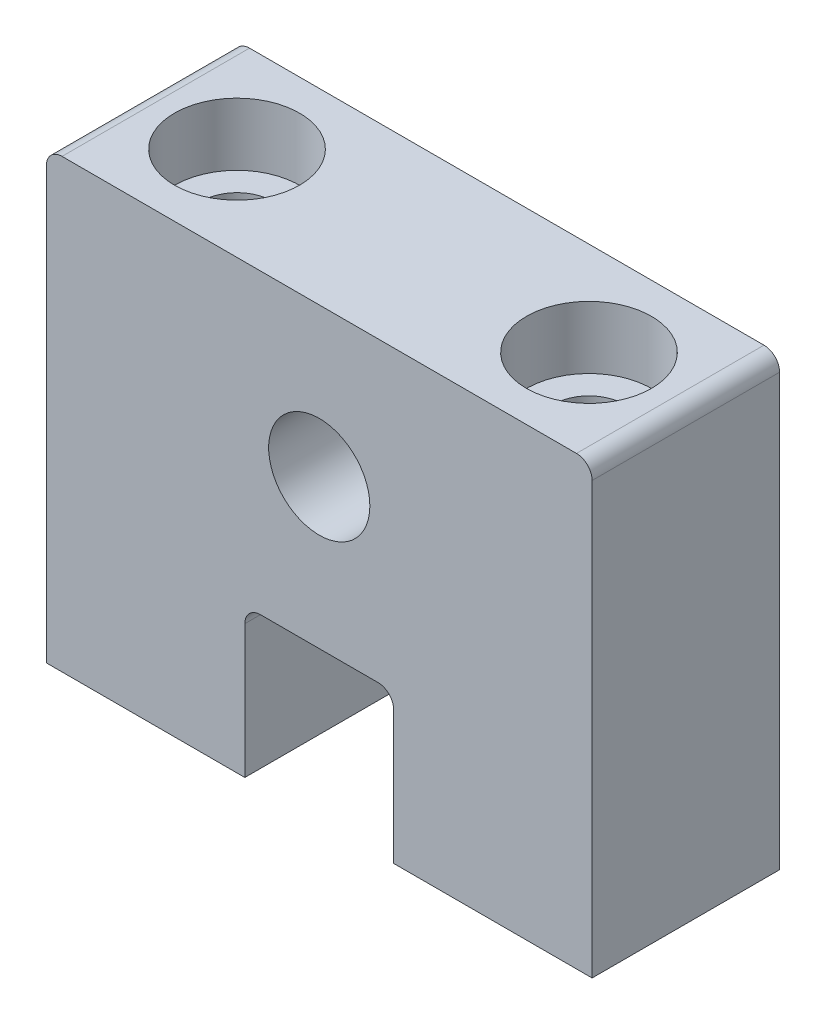
SolidWorks part; units mm, degrees
ref_plane "Front Plane" through (0, 0, 0) normal (0, 0, 1) x (1, 0, 0)
ref_plane "Top Plane" through (0, 0, 0) normal (0, 1, 0) x (1, 0, 0)
ref_plane "Right Plane" through (0, 0, 0) normal (1, 0, 0) x (0, 0, -1)
sketch "Sketch1" plane through (0, 0, 0) normal (0, 0, 1) x (1, 0, 0)
  line L0 (0, -26.1041) -> (0, 52.7781) construction
  line L1 (-17.4625, 28.575) -> (17.4625, 28.575)
  line L3 (-4.7625, 0) -> (-17.4625, 0)
  line L4 (17.4625, 0) -> (17.4625, 28.575)
  line L6 (-4.7625, 0) -> (-4.7625, 9.525)
  line L7 (-17.4625, 0) -> (-17.4625, 28.575)
  line L8 (4.7625, 0) -> (17.4625, 0)
  line L9 (-4.7625, 9.525) -> (4.7625, 9.525)
  line L10 (4.7625, 0) -> (4.7625, 9.525)
  circle A0 centre (0, 19.05) radius 3.2385
  point P15 (0, 15.8115)
  point P23 (4.7625, 4.7625)
  dimension "D6" = 6.477
  dimension "D3" = 9.525
  dimension "D2" = 19.05
  dimension "D1" = 28.575
  dimension "D4" = 9.525
  dimension "D7" = 34.925
extrude "Boss-Extrude1" add sketch "Sketch1" along normal blind 12
sketch "Sketch2" plane through (0, 28.575, 0) normal (0, 1, 0) x (1, 0, 0)
  line L0 (4.7625, -12) -> (4.7625, 0) construction
  line L1 (-4.7625, -12) -> (-4.7625, 0) construction
  line L2 (4.7625, -12) -> (4.7625, 0)
  line L3 (-4.7625, -12) -> (-4.7625, 0)
  line L4 (0, 0) -> (0, -12) construction
  line L5 (17.4625, 0) -> (-17.4625, 0) construction
  line L6 (17.4625, -12) -> (-17.4625, -12) construction
  line L7 (-17.4625, -6) -> (17.4625, -6) construction
  line L8 (-17.4625, -12) -> (-17.4625, 0) construction
  line L9 (17.4625, -12) -> (17.4625, 0) construction
  point P0 (-11.2625, -6)
  point P1 (11.2625, -6)
  dimension "D1" = 6.5
hole_wizard "CBORE for M4 SHCS1" positions "Sketch3" profile "Sketch4" counterbore size "M4" standard "ANSI Metric" end condition through all
sketch "Sketch3" plane through (0, 28.575, 0) normal (0, 1, 0) x (1, 0, 0)
  point P0 (-11.2625, -6)
  point P3 (11.2625, -6)
sketch "Sketch4" plane through (-11.2625, 28.575, 6) normal (1, 0, 0) x (0, 0, 1)
  line L0 (0, 0) -> (0, 28.575)
  line L1 (0, 28.575) -> (2.25, 28.575)
  line L3 (2.25, 28.575) -> (2.25, 4)
  line L4 (2.25, 4) -> (4, 4)
  line L5 (4, 4) -> (4, 0)
  line L7 (4, 0) -> (0, 0)
  line L11 (0, -6.35) -> (0, 107.95) construction
  dimension "Thru Hole Dia." = 4.5
  dimension "Thru Hole Depth" = 28.575
  dimension "C'Bore Dia." = 8
  dimension "C'Bore Depth" = 4
fillet "Fillet1" radius 1 4 edges at (4.7625, 9.525, 6) (-4.7625, 9.525, 6) (17.4625, 28.575, 6) (-17.4625, 28.575, 6)
equation "\"0.095inin\"=0.085"
